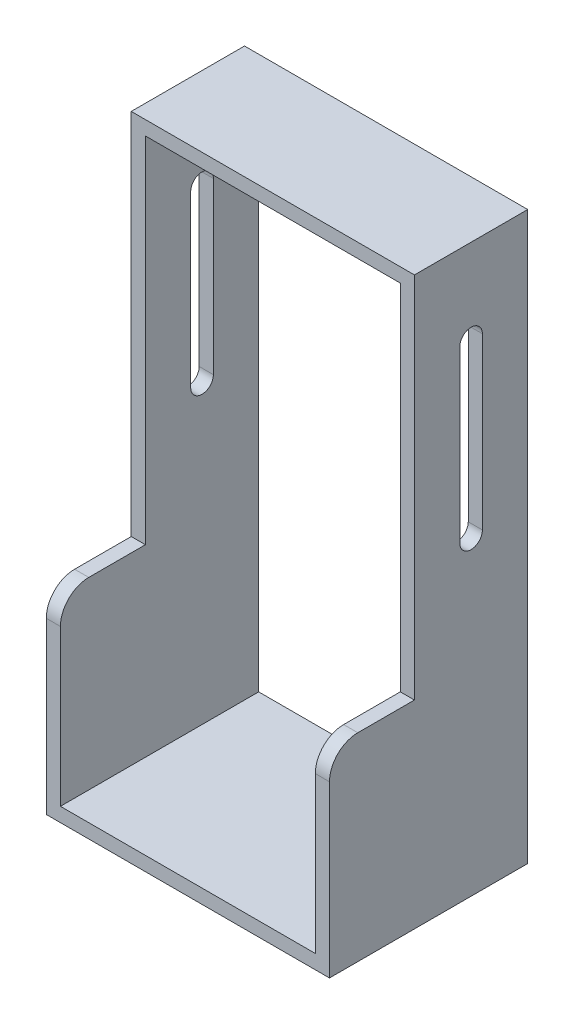
SolidWorks part; units mm, degrees
ref_plane "Front Plane" through (0, 0, 0) normal (0, 0, 1) x (1, 0, 0)
ref_plane "Top Plane" through (0, 0, 0) normal (0, 1, 0) x (1, 0, 0)
ref_plane "Right Plane" through (0, 0, 0) normal (1, 0, 0) x (0, 0, -1)
sketch "Sketch1" plane through (0, 0, 0) normal (0, 0, 1) x (1, 0, 0)
  line L1 (-50, -100) -> (50, -100)
  line L2 (-50, -100) -> (-50, 100)
  line L3 (-50, 100) -> (50, 100)
  line L4 (50, -100) -> (50, 100)
  line L5 (-50, -100) -> (50, 100) construction
  line L6 (-50, 100) -> (50, -100) construction
  line L7 (-45, -95) -> (45, -95)
  line L8 (-45, -95) -> (-45, 95)
  line L9 (-45, 95) -> (45, 95)
  line L10 (45, -95) -> (45, 95)
  line L11 (-45, -95) -> (45, 95) construction
  line L12 (-45, 95) -> (45, -95) construction
  point P0 (0, 0)
  point P6 (0, 0)
  dimension "D1" = 100
  dimension "D2" = 200
  dimension "D3" = 90
  dimension "D4" = 190
extrude "Boss-Extrude1" add sketch "Sketch1" along normal blind 70
sketch "Sketch2" plane through (50, 0, 0) normal (1, 0, 0) x (0, 0, -1)
  line L1 (-70, 100) -> (-40, 100)
  line L2 (-70, 100) -> (-70, -30)
  line L3 (-70, -30) -> (-40, -30)
  line L4 (-40, 100) -> (-40, -30)
  dimension "D1" = 130
  dimension "D2" = 30
extrude "Cut-Extrude1" cut sketch "Sketch2" against normal through all both and the other way through all
fillet "Fillet1" radius 10 2 edges at (47.5, -30, 70) (-47.5, -30, 70)
sketch "Sketch3" plane through (0, 95, 0) normal (0, -1, 0) x (1, 0, 0)
  line L0 (-50, 0) -> (50, 0) construction
  circle A0 centre (0, 15) radius 2.5
  point P4 (0, 0)
  dimension "D1" = 5
  dimension "D2" = 15
extrude "Boss-Extrude2" add sketch "Sketch3" along normal blind 5
sketch "Sketch4" plane through (-50, 0, 0) normal (-1, 0, 0) x (0, 0, 1)
  line L0 (20, 10) -> (20, 70) construction
  line L1 (16, 10) -> (16, 70)
  line L2 (24, 10) -> (24, 70)
  line L3 (40, 100) -> (0, 100) construction
  line L5 (0, 100) -> (0, -100) construction
  arc A0 (16, 10) -> (24, 10) centre (20, 10) ccw
  arc A1 (24, 70) -> (16, 70) centre (20, 70) ccw
  point P2 (20, 40)
  dimension "D1" = 8
  dimension "D2" = 60
  dimension "D3" = 30
  dimension "D4" = 20
extrude "Cut-Extrude2" cut sketch "Sketch4" against normal through all both
